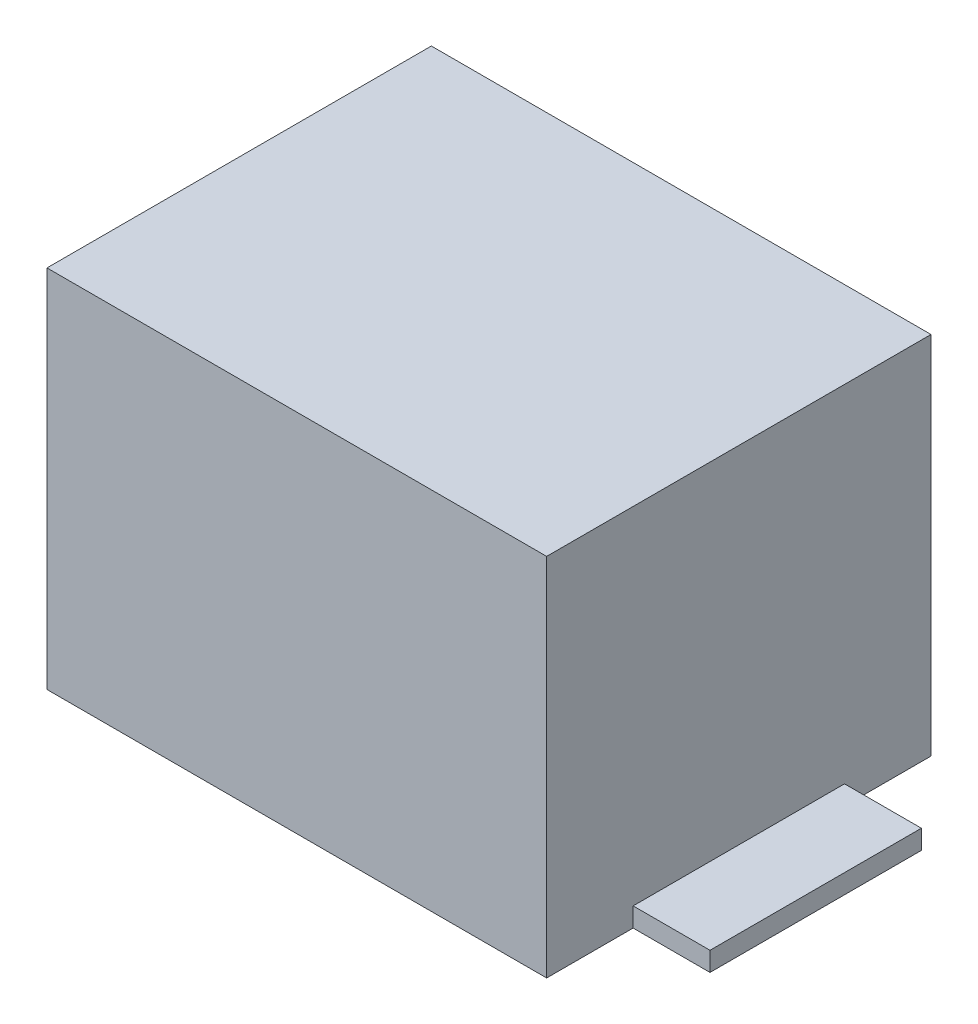
SolidWorks part; units mm, degrees
material "S235JR"
ref_plane "Vorderansicht (XY)" through (0, 0, 0) normal (0, 0, 1) x (1, 0, 0)
ref_plane "Draufansicht (XZ)" through (0, 0, 0) normal (0, 1, 0) x (1, 0, 0)
ref_plane "Seitenansicht (ZY)" through (0, 0, 0) normal (1, 0, 0) x (0, 0, -1)
sketch "Skizze1" plane through (0, 0, 0) normal (0, 1, 0) x (1, 0, 0)
  line L1 (-13, 10) -> (13, 10)
  line L2 (-13, 10) -> (-13, -10)
  line L3 (-13, -10) -> (13, -10)
  line L4 (13, 10) -> (13, -10)
  line L5 (-13, 10) -> (13, -10) construction
  line L6 (-13, -10) -> (13, 10) construction
  point P0 (0, 0)
  dimension "D1" = 26
  dimension "D2" = 20
extrude "Aufsatz-Linear austragen1" add sketch "Skizze1" along normal blind 19
sketch "Skizze2" plane through (0, 0, 0) normal (0, -1, 0) x (1, 0, 0)
  line L4 (-13, -10) -> (-13, 10) construction
  line L5 (-13, 0) -> (-17, 0) construction
  line L6 (-13, 5.5) -> (-13, -5.5)
  line L7 (-13, -5.5) -> (-17, -5.5)
  line L8 (-17, 5.5) -> (-17, -5.5)
  line L9 (-13, 5.5) -> (-17, 5.5)
  line L10 (0, 0) -> (0, 6.3486) construction
  line L11 (13, 0) -> (17, 0) construction
  line L12 (13, 5.5) -> (17, 5.5)
  line L13 (17, 5.5) -> (17, -5.5)
  line L14 (13, -5.5) -> (17, -5.5)
  line L15 (13, 5.5) -> (13, -5.5)
  point P10 (0, 0)
  dimension "D1" = 4
  dimension "D2" = 11
extrude "Aufsatz-Linear austragen2" add sketch "Skizze2" against normal blind 1 separate body
